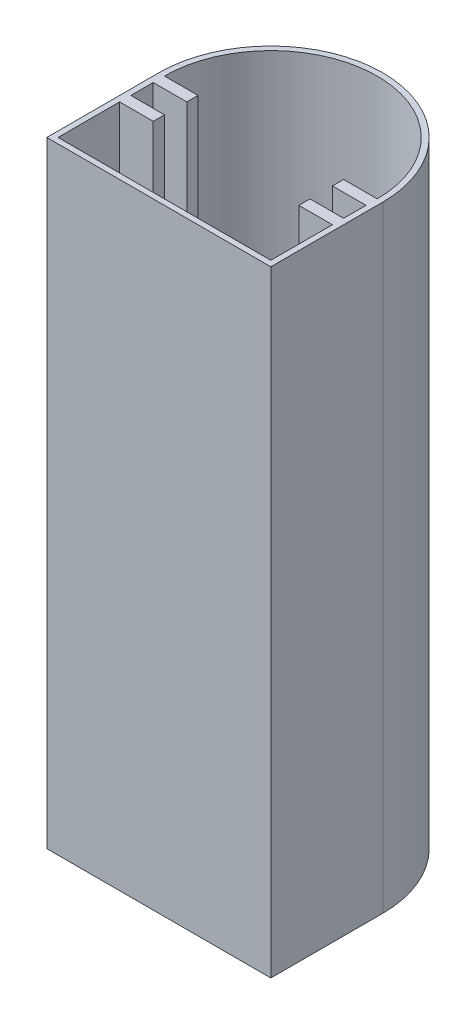
SolidWorks part; units mm, degrees
ref_plane "Front Plane" through (0, 0, 0) normal (0, 0, 1) x (1, 0, 0)
ref_plane "Top Plane" through (0, 0, 0) normal (0, 1, 0) x (1, 0, 0)
ref_plane "Right Plane" through (0, 0, 0) normal (1, 0, 0) x (0, 0, -1)
sketch "Sketch1" plane through (0, 0, 0) normal (0, 1, 0) x (1, 0, 0)
  line L0 (-38.8831, -1.7077) -> (1.1169, -1.7077)
  line L2 (-38.8831, -1.7077) -> (-38.8831, 18.2923)
  line L4 (1.1169, -1.7077) -> (1.1169, 18.2923)
  arc A0 (1.1169, 18.2923) -> (-38.8831, 18.2923) centre (-18.8831, 18.2923) ccw
  dimension "D3" = 20
  dimension "D1" = 40
  dimension "D2" = 20
extrude "Boss-Extrude1" add sketch "Sketch1" along normal blind 110 contours L2 A0 L4 L0
sketch "Sketch2" plane through (0, 110, 0) normal (0, 1, 0) x (1, 0, 0)
  line L5 (-37.8831, 16.2923) -> (-37.8831, 12.2923)
  line L6 (-37.8831, -0.7077) -> (0.1169, -0.7077)
  line L8 (-37.8831, 18.2923) -> (-31.8831, 18.2923)
  line L9 (-31.8831, 18.2923) -> (-31.8831, 16.2923)
  line L10 (-31.8831, 16.2923) -> (-37.8831, 16.2923)
  line L12 (-37.8831, 12.2923) -> (-31.8831, 12.2923)
  line L13 (-31.8831, 12.2923) -> (-31.8831, 10.2923)
  line L14 (-31.8831, 10.2923) -> (-37.8831, 10.2923)
  line L15 (0.1169, 10.2923) -> (0.1169, -0.7077)
  line L16 (-37.8831, 10.2923) -> (-37.8831, -0.7077)
  line L17 (-5.8831, 10.2923) -> (0.1169, 10.2923)
  line L18 (-5.8831, 12.2923) -> (-5.8831, 10.2923)
  line L19 (0.1169, 12.2923) -> (-5.8831, 12.2923)
  line L20 (-5.8831, 16.2923) -> (0.1169, 16.2923)
  line L21 (-5.8831, 18.2923) -> (-5.8831, 16.2923)
  line L22 (0.1169, 18.2923) -> (-5.8831, 18.2923)
  line L23 (-38.8831, -1.7077) -> (1.1169, -1.7077) construction
  line L24 (-38.8831, -1.7077) -> (-38.8831, 18.2923) construction
  line L25 (0.1169, 16.2923) -> (0.1169, 12.2923)
  arc A4 (0.1169, 18.2923) -> (-37.8831, 18.2923) centre (-18.8831, 18.2923) ccw
  point P7 (0, 0)
  point P8 (0, 0)
  point P25 (-18.8831, -0.7077)
  point P26 (0, 0)
  dimension "D13" = 19
  dimension "D1" = 6
  dimension "D2" = 2
  dimension "D3" = 4
  dimension "D4" = 2
  dimension "D5" = 6
  dimension "D6" = 1
  dimension "D7" = 1
  dimension "D8" = 6
  dimension "D9" = 4
  dimension "D10" = 2
  dimension "D11" = 2
  dimension "D12" = 1
  dimension "D14" = 6
extrude "Cut-Extrude1" cut sketch "Sketch2" against normal blind 109
sketch "Sketch3" plane through (-38.8831, 0, 0) normal (-1, 0, 0) x (0, 0, 1)
  line L0 (1.7077, 110) -> (1.7077, 0) construction
  line L1 (1.7077, 110) -> (-18.2923, 110) construction
  circle A0 centre (-4.9589, 55) radius 2.875
  point P4 (0, 0)
  dimension "D1" = 5.75
  dimension "D2" = 6.6667
  dimension "D3" = 55
extrude "Cut-Extrude2" cut sketch "Sketch3" against normal blind 5
equation "\"Width\" = 40"
equation "\"Depth\"= 20"
equation "\"lenght\"= 110"
equation "\"thick\"= 1"
equation "\"D1@Sketch1\"=\"Width\""
equation "\"D3@Sketch1\"=\"Width\"/2"
equation "\"length\"= 110"
equation "\"D1@Boss-Extrude1\"=\"length\""
equation "\"holder lenght\" = 6"
equation "\"holder width\"= 2"
equation "\"holder gap\"= 4"
equation "\"D1@Sketch2\"=\"holder lenght\""
equation "\"D2@Sketch2\"=\"holder width\""
equation "\"D3@Sketch2\"=\"holder gap\""
equation "\"D4@Sketch2\"=\"holder width\""
equation "\"D5@Sketch2\"=\"holder lenght\""
equation "\"D6@Sketch2\"=\"thick\""
equation "\"D7@Sketch2\"=\"thick\""
equation "\"D1@Cut-Extrude1\"=\"length\"-\"thick\""
equation "\"fillet\"= 0.5"
equation "\"D2@Sketch1\"=\"Depth\""
equation "\"D8@Sketch2\"=\"holder lenght\""
equation "\"D9@Sketch2\"=\"holder gap\""
equation "\"D10@Sketch2\"=\"holder width\""
equation "\"D11@Sketch2\"=\"holder width\""
equation "\"hole\"=5.75"
equation "\"D1@Sketch3\"=\"hole\""
equation "\"D2@Sketch3\"=\"Depth\"/3"
equation "\"D3@Sketch3\"=\"lenght\"/2"
equation "\"D12@Sketch2\"=\"thick\""
equation "\"D13@Sketch2\"=\"Width\"/2-\"thick\""
equation "\"D14@Sketch2\"=\"holder lenght\""
